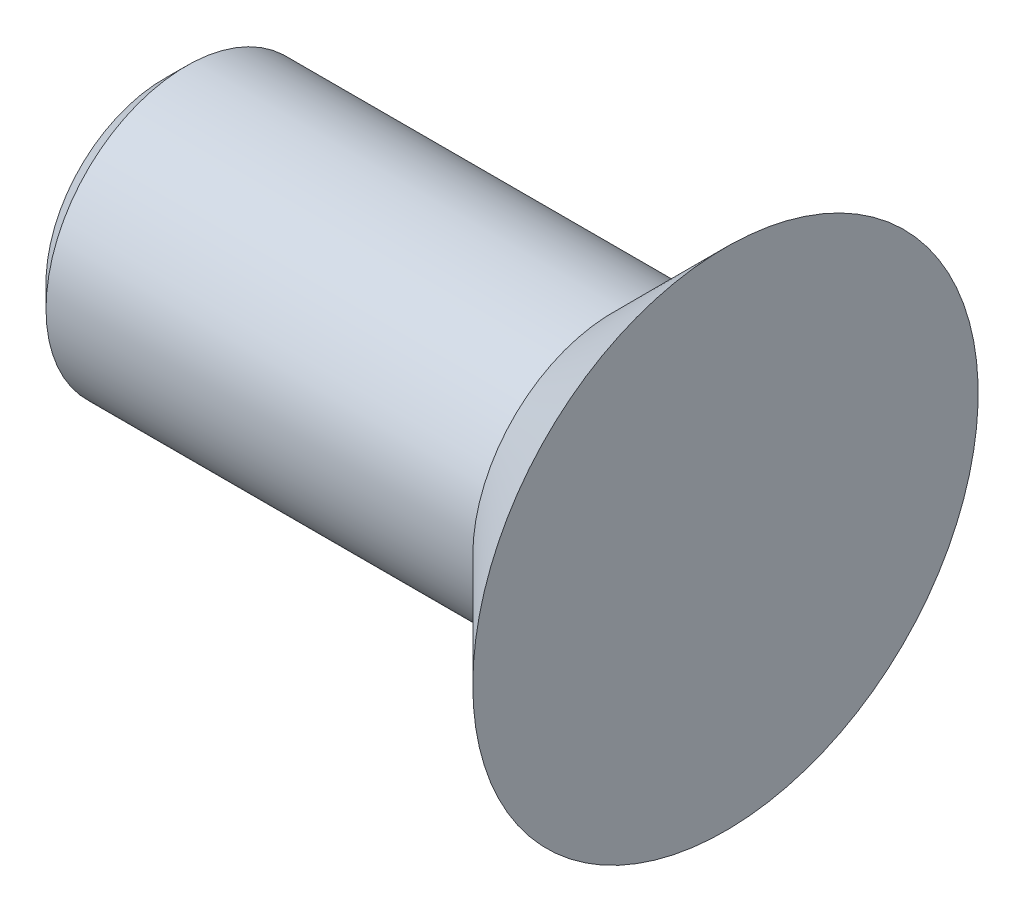
SolidWorks part; units mm, degrees
ref_plane "Plan de face" through (0, 0, 0) normal (0, 0, 1) x (1, 0, 0)
ref_plane "Plan de dessus" through (0, 0, 0) normal (0, 1, 0) x (1, 0, 0)
ref_plane "Plan de droite" through (0, 0, 0) normal (1, 0, 0) x (0, 0, -1)
sketch "Esquisse1" plane through (0, 0, 0) normal (0, 0, 1) x (1, 0, 0)
  line L0 (0, 0) -> (-10, 0)
  line L1 (-10, 0) -> (-10, 2.5)
  line L2 (-10, 2.5) -> (-2, 2.5)
  line L3 (-2, 2.5) -> (0, 4.5)
  line L4 (0, 4.5) -> (0, 0)
  line L5 (0, 0) -> (21.1509, 0) construction
  dimension "D1" = 45
  dimension "D2" = 2
  dimension "D3" = 5
  dimension "D4" = 10
revolve "Révolution1" add sketch "Esquisse1" angle 360 about L5
cosmetic thread "Représentation de filetage1" parameters "D2"=4.2
chamfer "Chanfrein1" distance 0.4 angle 45 1 edges at (-10, 0, 2.5)
